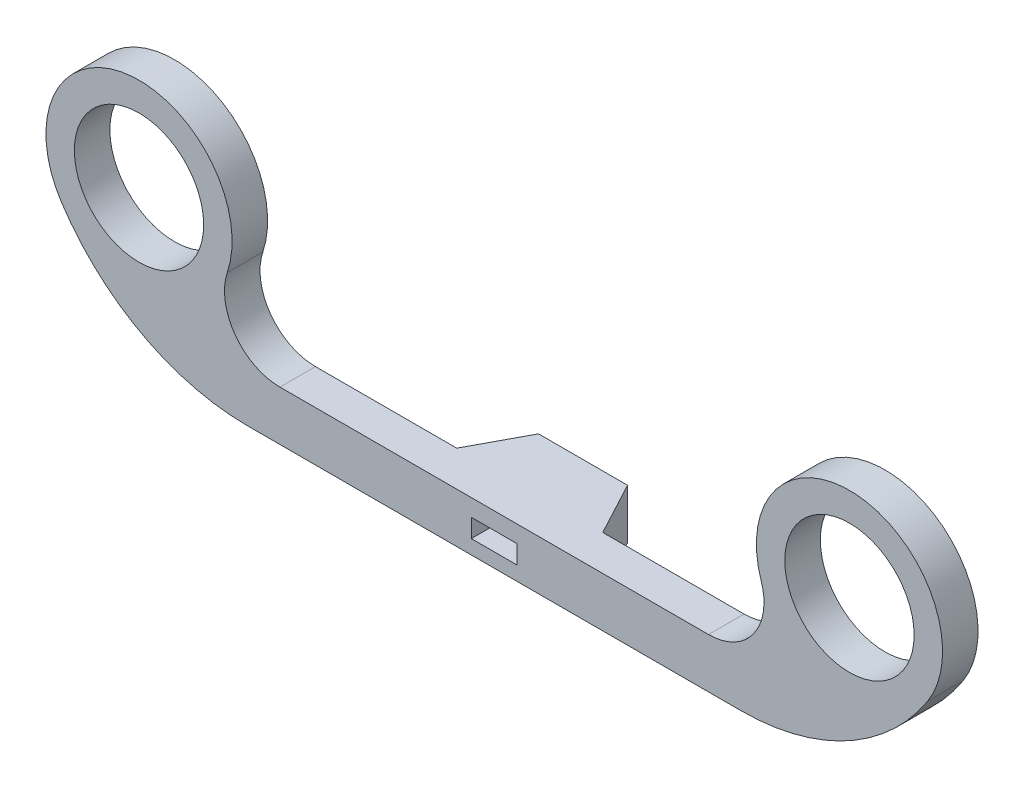
SolidWorks part; units mm, degrees
ref_plane "Front Plane" through (0, 0, 0) normal (0, 0, 1) x (1, 0, 0)
ref_plane "Top Plane" through (0, 0, 0) normal (0, 1, 0) x (1, 0, 0)
ref_plane "Right Plane" through (0, 0, 0) normal (1, 0, 0) x (0, 0, -1)
sketch "Sketch1" plane through (0, 0, 0) normal (0, 0, 1) x (1, 0, 0)
  line L0 (-22.0565, 18.161) -> (22.0565, 18.161)
  line L1 (-2.05, 21.082) -> (2.05, 21.082)
  line L2 (-2.05, 21.082) -> (-2.05, 19.431)
  line L3 (-2.05, 19.431) -> (2.05, 19.431)
  line L4 (2.05, 21.082) -> (2.05, 19.431)
  line L5 (-2.05, 21.082) -> (2.05, 19.431) construction
  line L6 (-2.05, 19.431) -> (2.05, 21.082) construction
  line L7 (-19.1516, 22.606) -> (19.1516, 22.606)
  circle A0 centre (-31.75, 31.75) radius 5.7785
  circle A1 centre (31.75, 31.75) radius 5.7785
  circle A2 centre (0, 0) radius 12.7 construction
  circle A3 centre (0, 0) radius 16.891 construction
  arc A4 (-23.856, 29.1267) -> (-38.7318, 27.2276) centre (-31.75, 31.75) ccw
  arc A5 (38.7318, 27.2276) -> (23.856, 29.1267) centre (31.75, 31.75) ccw
  arc A6 (19.1516, 22.606) -> (23.856, 29.1267) centre (19.1516, 27.5634) ccw
  arc A7 (-19.1516, 22.606) -> (-23.856, 29.1267) centre (-19.1516, 27.5634) cw
  arc A8 (-38.7318, 27.2276) -> (-22.0565, 18.161) centre (-22.0565, 38.0289) ccw
  arc A9 (22.0565, 18.161) -> (38.7318, 27.2276) centre (22.0565, 38.0289) ccw
  circle A11 centre (-31.75, 31.75) radius 8.3185 construction
  circle A12 centre (31.75, 31.75) radius 8.3185 construction
  point P8 (0, 20.2565)
  point P13 (0, 16.891)
  point P17 (25.02, 0)
  point P24 (0, 18.161)
  point P27 (0, 22.606)
  point P32 (-18.98, 0)
  dimension "D3" = 11.557
  dimension "D4" = 31.75
  dimension "D5" = 25.4
  dimension "D12" = 33.782
  dimension "D2" = 31.75
  dimension "D6" = 2.54
  dimension "D7" = 4.1
  dimension "D8" = 1.651
  dimension "D9" = 1.27
  dimension "D11" = 1.524
  dimension "D13" = 31.75
  dimension "D10" = 2.54
extrude "Boss-Extrude1" add sketch "Sketch1" along normal blind 12.7
sketch "Sketch2" plane through (0, 22.606, 0) normal (0, 1, 0) x (1, 0, 0)
  line L0 (-46.1574, -9.525) -> (-6.5247, -9.525)
  line L1 (-6.5247, -9.525) -> (-3.9786, -4.7625)
  line L2 (-3.9786, -4.7625) -> (3.9786, -4.7625)
  line L3 (3.9786, -4.7625) -> (6.5247, -9.525)
  line L4 (6.5247, -9.525) -> (46.1574, -9.525)
  line L5 (46.1574, -9.525) -> (46.1574, 7.6514)
  line L6 (46.1574, 7.6514) -> (-46.1574, 7.6514)
  line L7 (-46.1574, 7.6514) -> (-46.1574, -9.525)
  line L9 (19.1516, 0) -> (-19.1516, 0) construction
  line L10 (-40.0685, -12.7) -> (-23.4315, -12.7) construction
  point P8 (0, -4.7625)
  dimension "D1" = 3.175
  dimension "D2" = 4.7625
extrude "Cut-Extrude1" cut sketch "Sketch2" against normal up to next and the other way through all
equation "\"D2@Sketch1\"=\"D4@Sketch1\""
